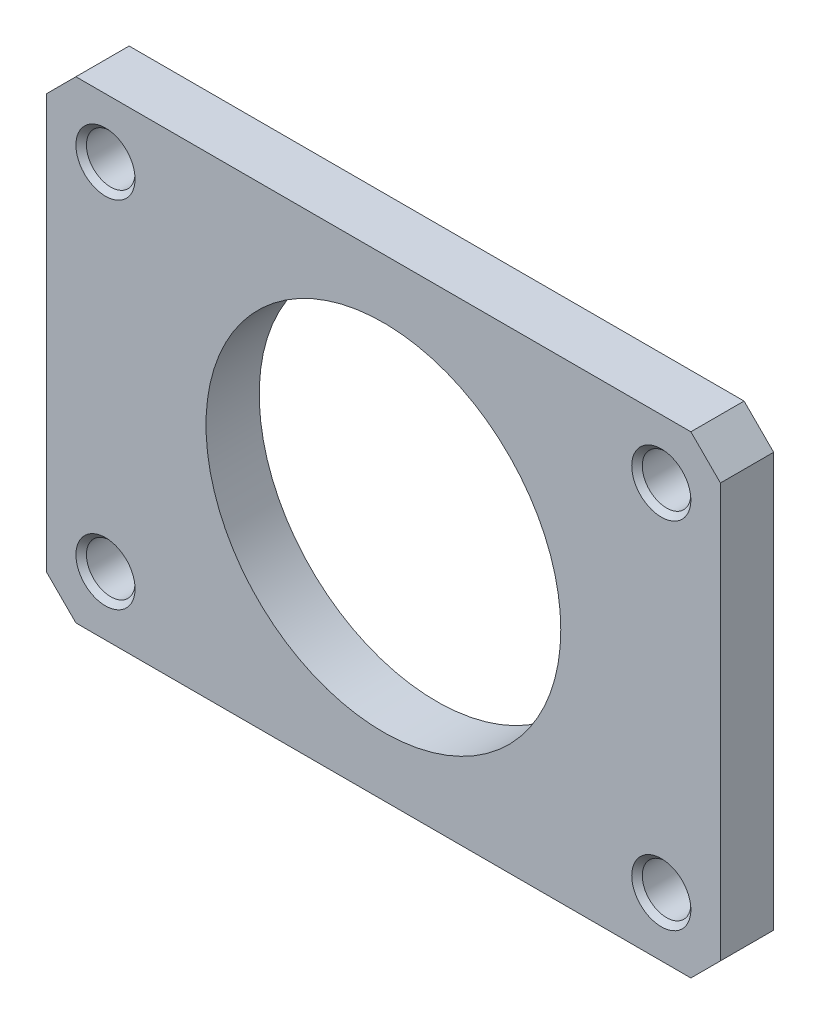
SolidWorks part; units mm, degrees
material "Сталь"
ref_plane "Спереди" through (0, 0, 0) normal (0, 0, 1) x (1, 0, 0)
ref_plane "Сверху" through (0, 0, 0) normal (0, 1, 0) x (1, 0, 0)
ref_plane "Справа" through (0, 0, 0) normal (1, 0, 0) x (0, 0, -1)
sketch "Эскиз1" plane through (0, 0, 0) normal (0, 0, 1) x (1, 0, 0)
  line L1 (-14.25, -10) -> (14.25, -10)
  line L2 (-14.25, -10) -> (-14.25, 10)
  line L3 (-14.25, 10) -> (14.25, 10)
  line L4 (14.25, -10) -> (14.25, 10)
  line L5 (-14.25, -10) -> (14.25, 10) construction
  line L6 (-14.25, 10) -> (14.25, -10) construction
  circle A0 centre (9.25, 5) radius 2.055
  point P0 (0, 0)
  dimension "D3" = 5
  dimension "D4" = 5
  dimension "D5" = 4.11
  dimension "D1" = 28.5
  dimension "D2" = 20
extrude "Бобышка-Вытянуть1" add sketch "Эскиз1" along normal blind 4.5
cosmetic thread "Условное изображение резьбы1" parameters "D2"=5
chamfer "Фаска1" distance 2.5 angle 45 1 edges at (14.25, 10, 2.25)
chamfer "Фаска2" distance 0.445 angle 45 2 edges at (11.305, 5, 0) (11.305, 5, 4.5)
mirror "Зеркальное отражение1" about plane through (-14.25, -10, 4.5) normal (0, 1, 0) of bodies 105
mirror "Зеркальное отражение2" about plane through (-14.25, -10, 4.5) normal (1, 0, 0) of bodies 106
sketch "Эскиз2" plane through (0, 0, 4.5) normal (0, 0, 1) x (1, 0, 0)
  line L0 (-42.75, -10) -> (14.25, -10) construction
  line L1 (-42.75, -27.5) -> (-42.75, 7.5) construction
  line L2 (14.25, -27.5) -> (14.25, 7.5) construction
  circle A0 centre (-14.25, -10) radius 15
  dimension "D1" = 30
extrude "Вырез-Вытянуть1" cut sketch "Эскиз2" against normal through all
